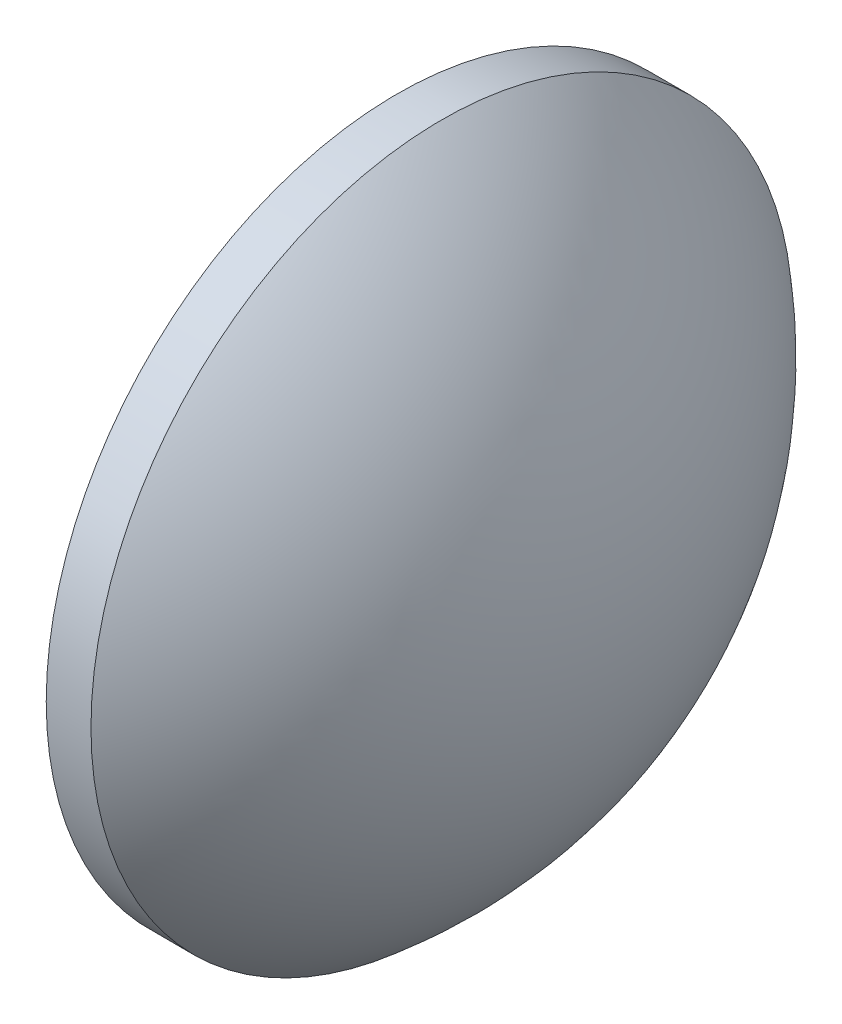
SolidWorks part; units mm, degrees
ref_plane "前视基准面" through (0, 0, 0) normal (0, 0, 1) x (1, 0, 0)
ref_plane "上视基准面" through (0, 0, 0) normal (0, 1, 0) x (1, 0, 0)
ref_plane "右视基准面" through (0, 0, 0) normal (1, 0, 0) x (0, 0, -1)
sketch "草图1" plane through (0, 0, 0) normal (0, 0, 1) x (1, 0, 0)
  line L0 (375.3642, -7.8338) -> (384.96, -7.8338) construction
  line L1 (377.0122, -7.8338) -> (377.0122, 0.1662)
  line L2 (377.0122, 0.1662) -> (378.0322, 0.1662)
  line L3 (381.8122, -7.8338) -> (377.0122, -7.8338)
  arc A0 (381.8122, -7.8338) -> (378.0322, 0.1662) centre (371.4566, -7.8338) ccw
revolve "旋转1" add sketch "草图1" angle 360 about L0
